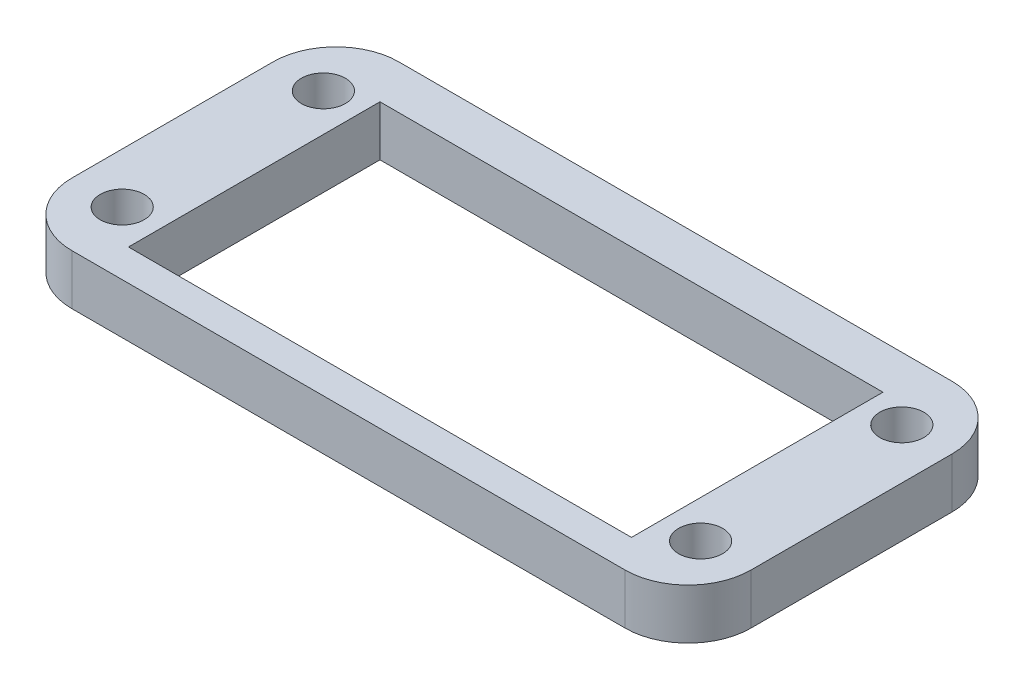
SolidWorks part; units mm, degrees
ref_plane "前视基准面" through (0, 0, 0) normal (0, 0, 1) x (1, 0, 0)
ref_plane "上视基准面" through (0, 0, 0) normal (0, 1, 0) x (1, 0, 0)
ref_plane "右视基准面" through (0, 0, 0) normal (1, 0, 0) x (0, 0, -1)
sketch "草图1" plane through (0, 0, 0) normal (0, 1, 0) x (1, 0, 0)
  line L0 (-55, 0) -> (55, 0) construction
  line L1 (-20, 9.5) -> (20, 9.5)
  line L2 (-20, 9.5) -> (-20, -10.5)
  line L3 (-20, -10.5) -> (20, -10.5)
  line L4 (20, 9.5) -> (20, -10.5)
  line L5 (-23, 8) -> (23, 8) construction
  line L6 (-23, 8) -> (-23, -8) construction
  line L7 (-23, -8) -> (23, -8) construction
  line L8 (23, 8) -> (23, -8) construction
  line L9 (0, -55) -> (0, 55) construction
  line L11 (-22, 13) -> (22, 13)
  line L12 (-27, 8) -> (-27, -8)
  line L13 (-22, -13) -> (22, -13)
  line L14 (27, 8) -> (27, -8)
  circle A0 centre (-23, -8) radius 1.75
  circle A1 centre (-23, 8) radius 1.75
  circle A2 centre (23, 8) radius 1.75
  circle A3 centre (23, -8) radius 1.75
  arc A4 (22, 13) -> (27, 8) centre (22, 8) cw
  arc A5 (27, -8) -> (22, -13) centre (22, -8) cw
  arc A6 (-27, -8) -> (-22, -13) centre (-22, -8) ccw
  arc A7 (-22, 13) -> (-27, 8) centre (-22, 8) ccw
  point P25 (27, -13)
  point P28 (-27, -13)
  dimension "D12" = 3.5
  dimension "D13" = 3.5
  dimension "D14" = 3.5
  dimension "D15" = 3.5
  dimension "D17" = 5
  dimension "D1" = 40
  dimension "D2" = 20
  dimension "D3" = 10.5
  dimension "D4" = 20
  dimension "D5" = 46
  dimension "D6" = 16
  dimension "D7" = 8
  dimension "D8" = 23
  dimension "D9" = 13
  dimension "D10" = 13
  dimension "D11" = 54
  dimension "D16" = 27
extrude "凸台-拉伸1" add sketch "草图1" along normal blind 4
